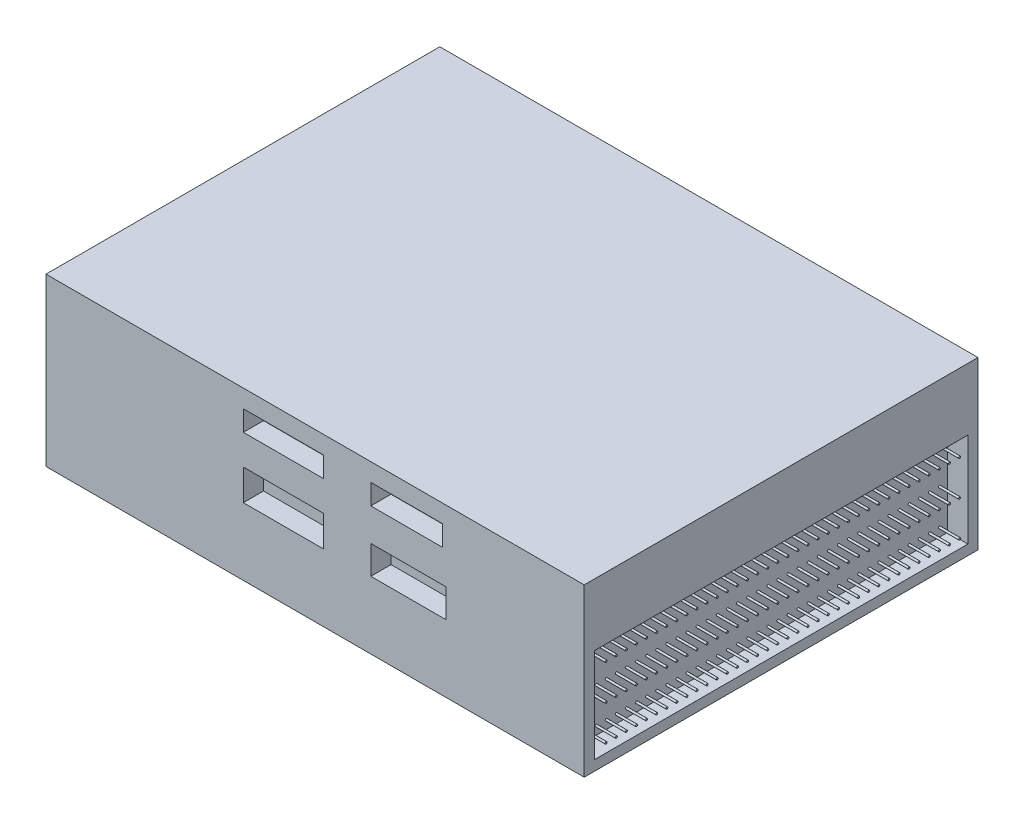
SolidWorks part; units mm, degrees
ref_plane "Front Plane" through (0, 0, 0) normal (0, 0, 1) x (1, 0, 0)
ref_plane "Top Plane" through (0, 0, 0) normal (0, 1, 0) x (1, 0, 0)
ref_plane "Right Plane" through (0, 0, 0) normal (1, 0, 0) x (0, 0, -1)
sketch "Sketch1" plane through (0, 0, 0) normal (0, 1, 0) x (1, 0, 0)
  line L1 (-26.65, 19.5) -> (26.65, 19.5)
  line L2 (-26.65, 19.5) -> (-26.65, -19.5)
  line L3 (-26.65, -19.5) -> (26.65, -19.5)
  line L4 (26.65, 19.5) -> (26.65, -19.5)
  point P4 (-26.65, 0)
  point P6 (0, 19.5)
  dimension "D1" = 39
  dimension "D2" = 53.3
extrude "Boss-Extrude1" add sketch "Sketch1" along normal blind 16.5
sketch "Sketch2" plane through (26.65, 0, 0) normal (1, 0, 0) x (0, 0, -1)
  line L0 (-19.5, 16.5) -> (-19.5, 0) construction
  line L1 (-18.5, 10.3502) -> (18.5, 10.3502)
  line L2 (-18.5, 10.3502) -> (-18.5, 1)
  line L3 (-18.5, 1) -> (18.5, 1)
  line L4 (18.5, 10.3502) -> (18.5, 1)
  line L5 (19.5, 16.5) -> (19.5, 0) construction
  line L6 (-19.5, 0) -> (19.5, 0) construction
  circle A0 centre (-17.3194, 8.8502) radius 0.1
  circle A1 centre (-17.3194, 5.3502) radius 0.1
  circle A2 centre (-17.3194, 1.8502) radius 0.1
  circle A3 centre (-16.3194, 8.8502) radius 0.1
  circle A4 centre (-16.3194, 5.3502) radius 0.1
  circle A5 centre (-16.3194, 1.8502) radius 0.1
  circle A6 centre (-15.3194, 8.8502) radius 0.1
  circle A7 centre (-15.3194, 5.3502) radius 0.1
  circle A8 centre (-15.3194, 1.8502) radius 0.1
  circle A9 centre (-14.3194, 8.8502) radius 0.1
  circle A10 centre (-14.3194, 5.3502) radius 0.1
  circle A11 centre (-14.3194, 1.8502) radius 0.1
  circle A12 centre (-13.3194, 8.8502) radius 0.1
  circle A13 centre (-13.3194, 5.3502) radius 0.1
  circle A14 centre (-13.3194, 1.8502) radius 0.1
  circle A15 centre (-12.3194, 8.8502) radius 0.1
  circle A16 centre (-12.3194, 5.3502) radius 0.1
  circle A17 centre (-12.3194, 1.8502) radius 0.1
  circle A18 centre (-11.3194, 8.8502) radius 0.1
  circle A19 centre (-11.3194, 5.3502) radius 0.1
  circle A20 centre (-11.3194, 1.8502) radius 0.1
  circle A21 centre (-10.3194, 8.8502) radius 0.1
  circle A22 centre (-10.3194, 5.3502) radius 0.1
  circle A23 centre (-10.3194, 1.8502) radius 0.1
  circle A24 centre (-9.3194, 8.8502) radius 0.1
  circle A25 centre (-9.3194, 5.3502) radius 0.1
  circle A26 centre (-9.3194, 1.8502) radius 0.1
  circle A27 centre (-8.3194, 8.8502) radius 0.1
  circle A28 centre (-8.3194, 5.3502) radius 0.1
  circle A29 centre (-8.3194, 1.8502) radius 0.1
  circle A30 centre (-7.3194, 8.8502) radius 0.1
  circle A31 centre (-7.3194, 5.3502) radius 0.1
  circle A32 centre (-7.3194, 1.8502) radius 0.1
  circle A33 centre (-6.3194, 8.8502) radius 0.1
  circle A34 centre (-6.3194, 5.3502) radius 0.1
  circle A35 centre (-6.3194, 1.8502) radius 0.1
  circle A36 centre (-5.3194, 8.8502) radius 0.1
  circle A37 centre (-5.3194, 5.3502) radius 0.1
  circle A38 centre (-5.3194, 1.8502) radius 0.1
  circle A39 centre (-4.3194, 8.8502) radius 0.1
  circle A40 centre (-4.3194, 5.3502) radius 0.1
  circle A41 centre (-4.3194, 1.8502) radius 0.1
  circle A42 centre (-3.3194, 8.8502) radius 0.1
  circle A43 centre (-3.3194, 5.3502) radius 0.1
  circle A44 centre (-3.3194, 1.8502) radius 0.1
  circle A45 centre (-2.3194, 8.8502) radius 0.1
  circle A46 centre (-2.3194, 5.3502) radius 0.1
  circle A47 centre (-2.3194, 1.8502) radius 0.1
  circle A48 centre (-1.3194, 8.8502) radius 0.1
  circle A49 centre (-1.3194, 5.3502) radius 0.1
  circle A50 centre (-1.3194, 1.8502) radius 0.1
  circle A51 centre (-0.3194, 8.8502) radius 0.1
  circle A52 centre (-0.3194, 5.3502) radius 0.1
  circle A53 centre (-0.3194, 1.8502) radius 0.1
  circle A54 centre (0.6806, 8.8502) radius 0.1
  circle A55 centre (0.6806, 5.3502) radius 0.1
  circle A56 centre (0.6806, 1.8502) radius 0.1
  circle A57 centre (1.6806, 8.8502) radius 0.1
  circle A58 centre (1.6806, 5.3502) radius 0.1
  circle A59 centre (1.6806, 1.8502) radius 0.1
  circle A60 centre (2.6806, 8.8502) radius 0.1
  circle A61 centre (2.6806, 5.3502) radius 0.1
  circle A62 centre (2.6806, 1.8502) radius 0.1
  circle A63 centre (3.6806, 8.8502) radius 0.1
  circle A64 centre (3.6806, 5.3502) radius 0.1
  circle A65 centre (3.6806, 1.8502) radius 0.1
  circle A66 centre (4.6806, 8.8502) radius 0.1
  circle A67 centre (4.6806, 5.3502) radius 0.1
  circle A68 centre (4.6806, 1.8502) radius 0.1
  circle A69 centre (5.6806, 8.8502) radius 0.1
  circle A70 centre (5.6806, 5.3502) radius 0.1
  circle A71 centre (5.6806, 1.8502) radius 0.1
  circle A72 centre (6.6806, 8.8502) radius 0.1
  circle A73 centre (6.6806, 5.3502) radius 0.1
  circle A74 centre (6.6806, 1.8502) radius 0.1
  circle A75 centre (7.6806, 8.8502) radius 0.1
  circle A76 centre (7.6806, 5.3502) radius 0.1
  circle A77 centre (7.6806, 1.8502) radius 0.1
  circle A78 centre (8.6806, 8.8502) radius 0.1
  circle A79 centre (8.6806, 5.3502) radius 0.1
  circle A80 centre (8.6806, 1.8502) radius 0.1
  circle A81 centre (9.6806, 8.8502) radius 0.1
  circle A82 centre (9.6806, 5.3502) radius 0.1
  circle A83 centre (9.6806, 1.8502) radius 0.1
  circle A84 centre (10.6806, 8.8502) radius 0.1
  circle A85 centre (10.6806, 5.3502) radius 0.1
  circle A86 centre (10.6806, 1.8502) radius 0.1
  circle A87 centre (11.6806, 8.8502) radius 0.1
  circle A88 centre (11.6806, 5.3502) radius 0.1
  circle A89 centre (11.6806, 1.8502) radius 0.1
  circle A90 centre (12.6806, 8.8502) radius 0.1
  circle A91 centre (12.6806, 5.3502) radius 0.1
  circle A92 centre (12.6806, 1.8502) radius 0.1
  circle A93 centre (13.6806, 8.8502) radius 0.1
  circle A94 centre (13.6806, 5.3502) radius 0.1
  circle A95 centre (13.6806, 1.8502) radius 0.1
  circle A96 centre (14.6806, 8.8502) radius 0.1
  circle A97 centre (14.6806, 5.3502) radius 0.1
  circle A98 centre (14.6806, 1.8502) radius 0.1
  circle A99 centre (15.6806, 8.8502) radius 0.1
  circle A100 centre (15.6806, 5.3502) radius 0.1
  circle A101 centre (15.6806, 1.8502) radius 0.1
  circle A102 centre (16.6806, 8.8502) radius 0.1
  circle A103 centre (16.6806, 5.3502) radius 0.1
  circle A104 centre (16.6806, 1.8502) radius 0.1
  circle A105 centre (17.6806, 8.8502) radius 0.1
  circle A106 centre (17.6806, 5.3502) radius 0.1
  circle A107 centre (17.6806, 1.8502) radius 0.1
  dimension "D7" = 0.2
  dimension "D1" = 1
  dimension "D2" = 1
  dimension "D3" = 1
  dimension "D4" = 3.5
  dimension "D5" = 3.5
  dimension "D6" = 1.5
  dimension "D8" = 36
extrude "Cut-Extrude1" cut sketch "Sketch2" against normal blind 2
sketch "Sketch3" plane through (-26.65, 0, 0) normal (-1, 0, 0) x (0, 0, 1)
  line L1 (-16.9048, 6.9306) -> (-10.137, 6.9306)
  line L2 (-16.9048, 6.9306) -> (-16.9048, 9.1056)
  line L3 (-16.9048, 9.1056) -> (-10.137, 9.1056)
  line L4 (-10.137, 6.9306) -> (-10.137, 9.1056)
  line L5 (-16.9048, 5.7252) -> (-7.4358, 5.7252)
  line L6 (-16.9048, 5.7252) -> (-16.9048, 2.7916)
  line L7 (-16.9048, 2.7916) -> (-7.4358, 2.7916)
  line L8 (-7.4358, 5.7252) -> (-7.4358, 2.7916)
  line L9 (-5.8557, 9.1056) -> (4.0153, 9.1056)
  line L10 (-5.8557, 9.1056) -> (-5.8557, 6.9306)
  line L11 (-5.8557, 6.9306) -> (4.0153, 6.9306)
  line L12 (4.0153, 9.1056) -> (4.0153, 6.9306)
  line L13 (6.6504, 9.1056) -> (17.8598, 9.1056)
  line L14 (6.6504, 9.1056) -> (6.6504, 6.9306)
  line L15 (6.6504, 6.9306) -> (17.8598, 6.9306)
  line L16 (17.8598, 9.1056) -> (17.8598, 6.9306)
  line L17 (-5.8557, 5.7252) -> (4.0153, 5.7252)
  line L18 (-5.8557, 5.7252) -> (-5.8557, 2.7916)
  line L19 (-5.8557, 2.7916) -> (4.0153, 2.7916)
  line L20 (4.0153, 5.7252) -> (4.0153, 2.7916)
  line L21 (6.6922, 5.7252) -> (17.8598, 5.7252)
  line L22 (6.6922, 5.7252) -> (6.6922, 2.7916)
  line L23 (6.6922, 2.7916) -> (17.8598, 2.7916)
  line L24 (17.8598, 5.7252) -> (17.8598, 2.7916)
extrude "Cut-Extrude2" cut sketch "Sketch3" against normal blind 2
sketch "Sketch4" plane through (0, 0, -19.5) normal (0, 0, -1) x (-1, 0, 0)
  line L1 (-1.6275, 15.1419) -> (5.0017, 15.1419)
  line L2 (-1.6275, 15.1419) -> (-1.6275, 12.9586)
  line L3 (-1.6275, 12.9586) -> (5.0017, 12.9586)
  line L4 (5.0017, 15.1419) -> (5.0017, 12.9586)
  line L5 (11.9485, 15.1419) -> (19.7687, 15.1419)
  line L6 (11.9485, 15.1419) -> (11.9485, 12.9586)
  line L7 (11.9485, 12.9586) -> (19.7687, 12.9586)
  line L8 (19.7687, 15.1419) -> (19.7687, 12.9586)
extrude "Cut-Extrude3" cut sketch "Sketch4" against normal blind 2
sketch "Sketch5" plane through (0, 0, 19.5) normal (0, 0, 1) x (1, 0, 0)
  line L1 (-7.1056, 14.7282) -> (0.8336, 14.7282)
  line L2 (-7.1056, 14.7282) -> (-7.1056, 12.7037)
  line L3 (-7.1056, 12.7037) -> (0.8336, 12.7037)
  line L4 (0.8336, 14.7282) -> (0.8336, 12.7037)
  line L5 (-7.1056, 9.7265) -> (0.8336, 9.7265)
  line L6 (-7.1056, 9.7265) -> (-7.1056, 6.6699)
  line L7 (-7.1056, 6.6699) -> (0.8336, 6.6699)
  line L8 (0.8336, 9.7265) -> (0.8336, 6.6699)
  line L9 (5.5178, 14.7282) -> (12.6234, 14.7282)
  line L10 (5.5178, 14.7282) -> (5.5178, 12.7037)
  line L11 (5.5178, 12.7037) -> (12.6234, 12.7037)
  line L12 (12.6234, 14.7282) -> (12.6234, 12.7037)
  line L13 (5.5178, 9.4883) -> (12.941, 9.4883)
  line L14 (5.5178, 9.4883) -> (5.5178, 6.6699)
  line L15 (5.5178, 6.6699) -> (12.941, 6.6699)
  line L16 (12.941, 9.4883) -> (12.941, 6.6699)
extrude "Cut-Extrude4" cut sketch "Sketch5" against normal blind 2
